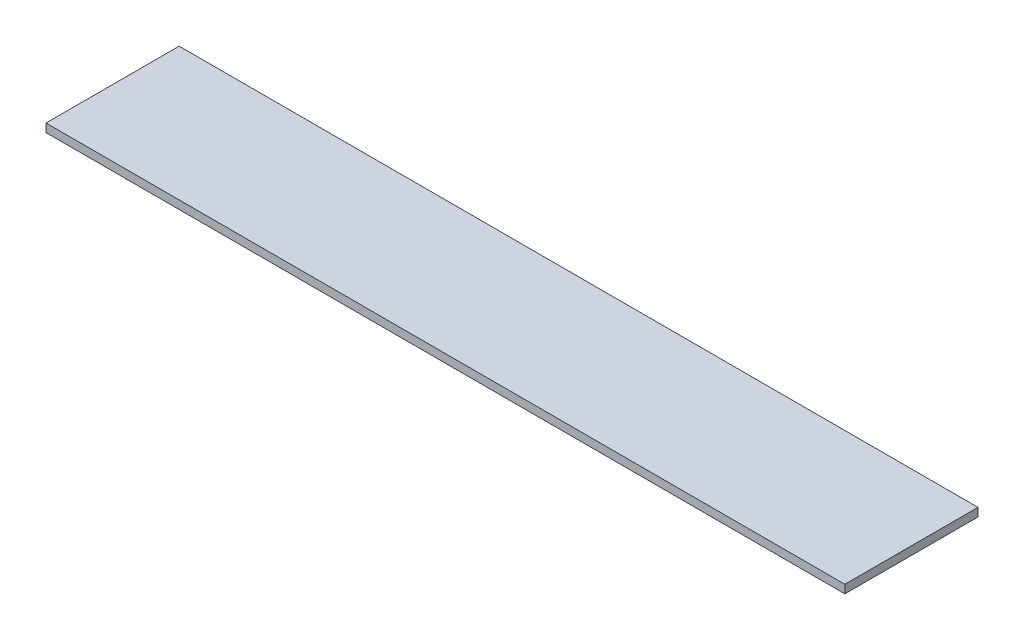
SolidWorks part; units mm, degrees
material "Nylon 101"
ref_plane "Front Plane" through (0, 0, 0) normal (0, 0, 1) x (1, 0, 0)
ref_plane "Top Plane" through (0, 0, 0) normal (0, 1, 0) x (1, 0, 0)
ref_plane "Right Plane" through (0, 0, 0) normal (1, 0, 0) x (0, 0, -1)
sketch "Sketch2" plane through (0, 0, 0) normal (0, 1, 0) x (1, 0, 0)
  line L1 (0, 0) -> (152.4, 0)
  line L2 (0, 0) -> (0, 25.4)
  line L3 (0, 25.4) -> (152.4, 25.4)
  line L4 (152.4, 0) -> (152.4, 25.4)
  dimension "D1" = 25.4
  dimension "D2" = 152.4
extrude "Boss-Extrude1" add sketch "Sketch2" along normal blind 1.5875
